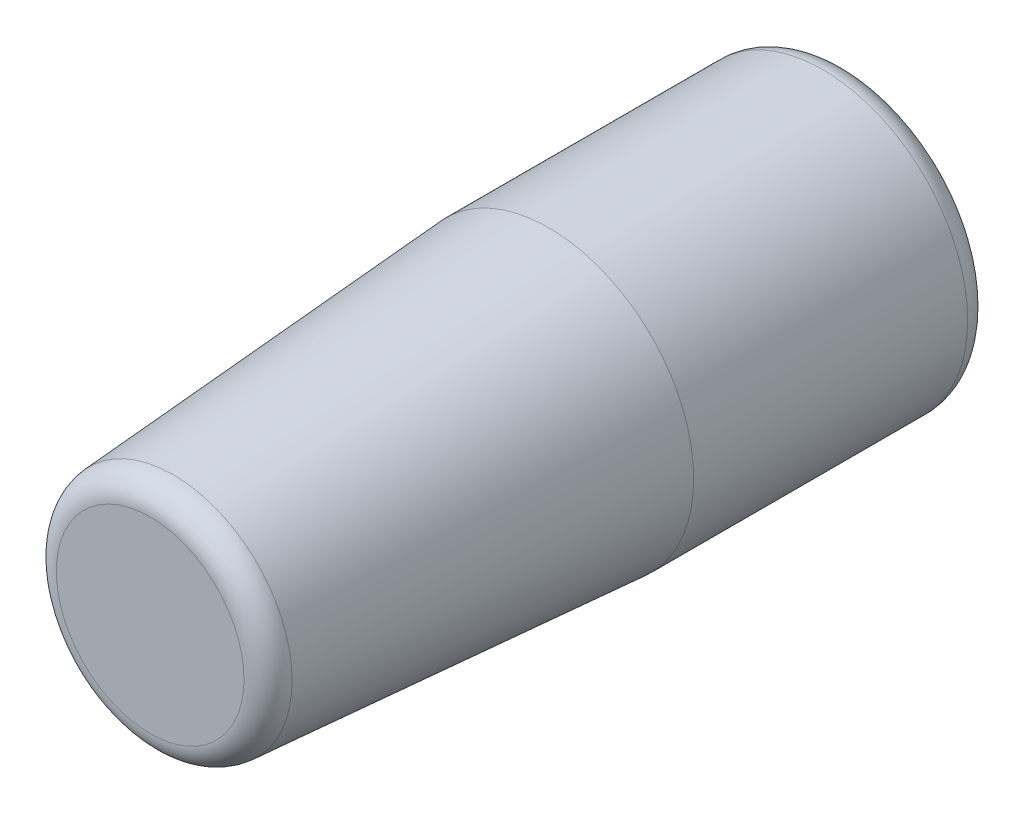
SolidWorks part; units mm, degrees
ref_plane "Front Plane" through (0, 0, 0) normal (0, 0, 1) x (1, 0, 0)
ref_plane "Top Plane" through (0, 0, 0) normal (0, 1, 0) x (1, 0, 0)
ref_plane "Right Plane" through (0, 0, 0) normal (1, 0, 0) x (0, 0, -1)
sketch "Sketch1" plane through (0, 0, 0) normal (0, 0, 1) x (1, 0, 0)
  circle A1 centre (0, 0) radius 73.914
extrude "Boss-Extrude1" add sketch "Sketch1" along normal blind 152.4
sketch "Sketch2" plane through (0, 0, 152.4) normal (0, 0, 1) x (1, 0, 0)
  circle A0 centre (0, 0) radius 73.914
extrude "Boss-Extrude2" add sketch "Sketch2" along normal blind 203.2 draft 4
fillet "Fillet1" radius 12.7 2 edges at (73.914, 0, 0) (59.7049, 0, 355.6)
